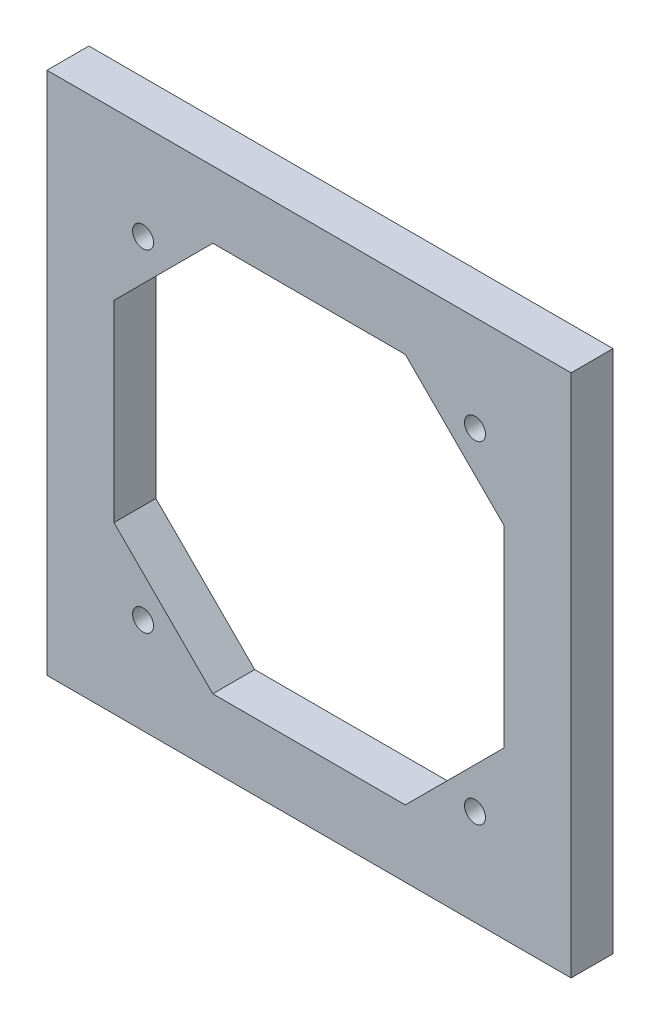
SolidWorks part; units mm, degrees
ref_plane "Front Plane" through (0, 0, 0) normal (0, 0, 1) x (1, 0, 0)
ref_plane "Top Plane" through (0, 0, 0) normal (0, 1, 0) x (1, 0, 0)
ref_plane "Right Plane" through (0, 0, 0) normal (1, 0, 0) x (0, 0, -1)
sketch "Sketch1" plane through (0, 0, 0) normal (0, 0, 1) x (1, 0, 0)
  line L0 (-23.75, 23.75) -> (23.75, -23.75) construction
  line L1 (37.5, -37.5) -> (-37.5, -37.5)
  line L2 (37.5, -37.5) -> (37.5, 37.5)
  line L3 (37.5, 37.5) -> (-37.5, 37.5)
  line L4 (-37.5, -37.5) -> (-37.5, 37.5)
  line L5 (37.5, -37.5) -> (-37.5, 37.5) construction
  line L6 (37.5, 37.5) -> (-37.5, -37.5) construction
  line L7 (-23.75, -23.75) -> (23.75, 23.75) construction
  line L8 (-26.5, 12.3579) -> (-12.3579, 26.5) construction
  line L9 (26.5, -26.5) -> (-26.5, -26.5) construction
  line L10 (26.5, -26.5) -> (26.5, 26.5) construction
  line L11 (26.5, 26.5) -> (-26.5, 26.5) construction
  line L12 (-26.5, -26.5) -> (-26.5, 26.5) construction
  line L13 (26.5, -26.5) -> (-26.5, 26.5) construction
  line L14 (26.5, 26.5) -> (-26.5, -26.5) construction
  line L15 (12.3579, 26.5) -> (26.5, 12.3579) construction
  line L16 (-26.5, -12.3579) -> (-12.3579, -26.5) construction
  line L17 (26.5, -12.3579) -> (12.3579, -26.5) construction
  line L18 (-27.9142, 13.7721) -> (-13.7721, 27.9142)
  line L19 (27.9142, -13.7721) -> (13.7721, -27.9142)
  line L20 (-27.9142, -13.7721) -> (-13.7721, -27.9142)
  line L21 (13.7721, 27.9142) -> (27.9142, 13.7721)
  line L22 (-27.9142, 13.7721) -> (-27.9142, -13.7721)
  line L23 (-13.7721, -27.9142) -> (13.7721, -27.9142)
  line L24 (27.9142, -13.7721) -> (27.9142, 13.7721)
  line L25 (13.7721, 27.9142) -> (-13.7721, 27.9142)
  circle A0 centre (-23.75, 23.75) radius 1.5
  circle A1 centre (23.75, 23.75) radius 1.5
  circle A2 centre (23.75, -23.75) radius 1.5
  circle A3 centre (-23.75, -23.75) radius 1.5
  point P0 (0, 0)
  point P14 (0, 0)
  point P15 (0, 0)
  dimension "D1" = 3
  dimension "D2" = 47.5
  dimension "D3" = 47.5
  dimension "D4" = 53
  dimension "D5" = 45
  dimension "D6" = 20
  dimension "D7" = 45
  dimension "D8" = 45
  dimension "D9" = 45
  dimension "D13" = 75
  dimension "D10" = 2
  dimension "D11" = 2
  dimension "D12" = 2
extrude "Boss-Extrude1" add sketch "Sketch1" along normal blind 6
